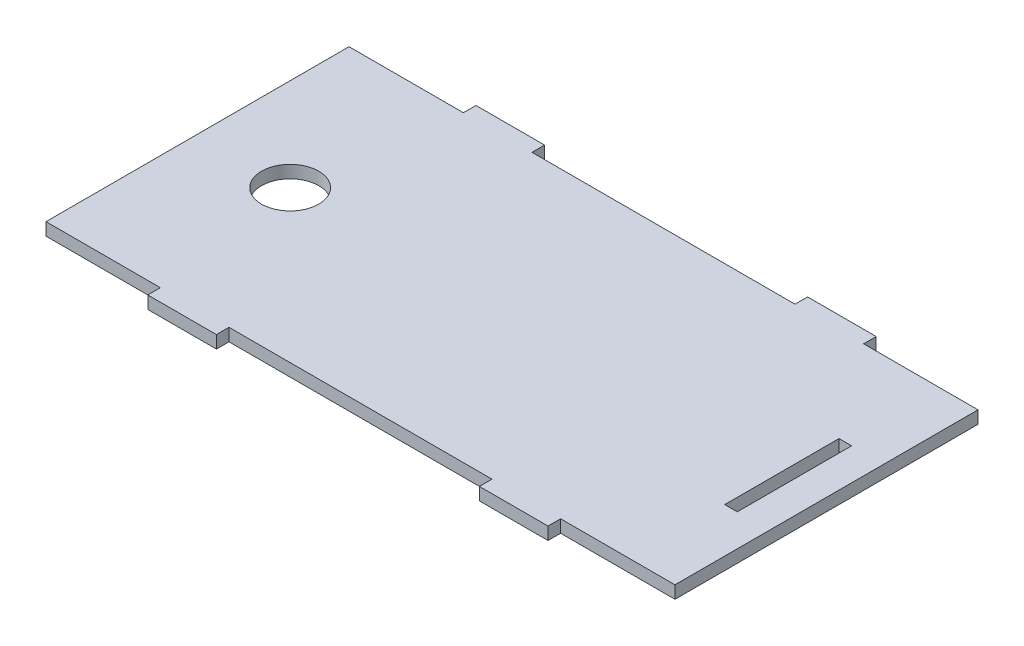
SolidWorks part; units mm, degrees
ref_plane "Front Plane" through (0, 0, 0) normal (0, 0, 1) x (1, 0, 0)
ref_plane "Top Plane" through (0, 0, 0) normal (0, 1, 0) x (1, 0, 0)
ref_plane "Right Plane" through (0, 0, 0) normal (1, 0, 0) x (0, 0, -1)
sketch "Sketch2" plane through (0, 0, 0) normal (0, 1, 0) x (1, 0, 0)
  line L0 (145.6909, 33.655) -> (5.9909, 33.655) construction
  line L1 (0, 0) -> (25.4, 0)
  line L2 (0, 0) -> (0, 67.31)
  line L3 (0, 67.31) -> (25.4, 67.31)
  line L4 (139.7, 0) -> (139.7, 67.31)
  line L5 (40.64, 67.31) -> (99.06, 67.31)
  line L6 (132.588, 20.955) -> (129.794, 20.955)
  line L7 (132.588, 20.955) -> (132.588, 46.355)
  line L8 (132.588, 46.355) -> (129.794, 46.355)
  line L9 (129.794, 20.955) -> (129.794, 46.355)
  line L10 (132.588, 20.955) -> (129.794, 46.355) construction
  line L11 (132.588, 46.355) -> (129.794, 20.955) construction
  line L12 (25.4, 70.104) -> (40.64, 70.104)
  line L13 (25.4, 70.104) -> (25.4, 67.31)
  line L14 (40.64, 0) -> (99.06, 0)
  line L15 (40.64, 70.104) -> (40.64, 67.31)
  line L16 (99.06, 70.104) -> (114.3, 70.104)
  line L17 (99.06, 70.104) -> (99.06, 67.31)
  line L18 (114.3, 0) -> (139.7, 0)
  line L19 (114.3, 70.104) -> (114.3, 67.31)
  line L20 (114.3, 67.31) -> (139.7, 67.31)
  line L21 (25.4, 0) -> (25.4, -2.794)
  line L22 (25.4, -2.794) -> (40.64, -2.794)
  line L23 (40.64, 0) -> (40.64, -2.794)
  line L25 (99.06, 0) -> (99.06, -2.794)
  line L26 (99.06, -2.794) -> (114.3, -2.794)
  line L27 (114.3, 0) -> (114.3, -2.794)
  circle A0 centre (20.574, 33.655) radius 6.35
  point P6 (133.6478, 33.655)
  point P11 (129.794, 33.655)
  point P12 (132.588, 33.655)
  dimension "D11" = 12.7
  dimension "D1" = 139.7
  dimension "D2" = 67.31
  dimension "D3" = 2.794
  dimension "D4" = 25.4
  dimension "D5" = 129.794
  dimension "D6" = 2.794
  dimension "D7" = 15.24
  dimension "D8" = 25.4
  dimension "D9" = 15.24
  dimension "D10" = 58.42
  dimension "D12" = 109.22
extrude "Boss-Extrude1" add sketch "Sketch2" along normal blind 2.794
